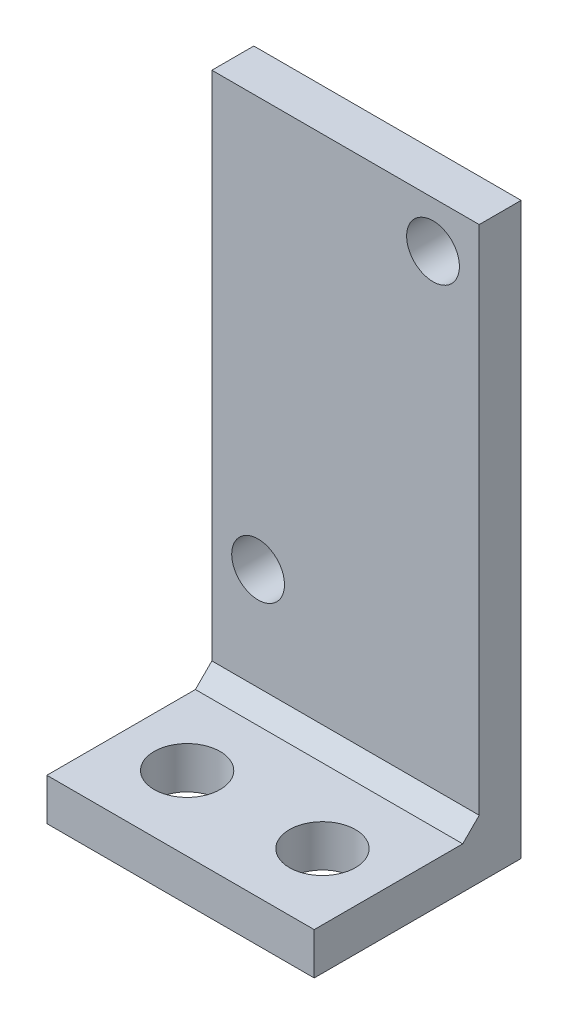
SolidWorks part; units mm, degrees
ref_plane "Front Plane" through (0, 0, 0) normal (0, 0, 1) x (1, 0, 0)
ref_plane "Top Plane" through (0, 0, 0) normal (0, 1, 0) x (1, 0, 0)
ref_plane "Right Plane" through (0, 0, 0) normal (1, 0, 0) x (0, 0, -1)
sketch "Sketch1" plane through (0, 0, 0) normal (0, 0, 1) x (1, 0, 0)
  line L1 (0, 0) -> (16.2, 0)
  line L2 (0, 0) -> (0, 34.54)
  line L3 (0, 34.54) -> (16.2, 34.54)
  line L4 (16.2, 0) -> (16.2, 34.54)
  dimension "D1" = 16.2
  dimension "D2" = 34.54
extrude "Boss-Extrude1" add sketch "Sketch1" along normal blind 2.54
sketch "Sketch2" plane through (0, 0, 2.54) normal (0, 0, 1) x (1, 0, 0)
  line L0 (16.2, 0) -> (16.2, 34.54) construction
  line L1 (0, 0) -> (16.2, 0)
  line L2 (0, 0) -> (0, 2.54)
  line L3 (0, 2.54) -> (16.2, 2.54)
  line L4 (16.2, 0) -> (16.2, 2.54)
  dimension "D1" = 2.54
extrude "Boss-Extrude2" add sketch "Sketch2" along normal blind 10
chamfer "Chamfer1" distance 1 angle 45 1 edges at (8.1, 2.54, 2.54)
sketch "Sketch4" plane through (0, 0, 0) normal (0, 0, -1) x (-1, 0, 0)
  line L0 (-16.2, 0) -> (-16.2, 34.54) construction
  line L1 (-16.2, 34.54) -> (0, 34.54) construction
  line L2 (0, 34.54) -> (0, 0) construction
  circle A0 centre (-13.4, 31.74) radius 1.6
  circle A1 centre (-2.8, 9.74) radius 1.6
  dimension "D1" = 3.2
  dimension "D2" = 2.8
  dimension "D3" = 2.8
  dimension "D4" = 2.8
  dimension "D5" = 22
extrude "Cut-Extrude1" cut sketch "Sketch4" against normal blind 2.54
sketch "Sketch5" plane through (0, 2.54, 0) normal (0, 1, 0) x (1, 0, 0)
  line L0 (16.2, -8.04) -> (0, -8.04) construction
  line L1 (16.2, -12.54) -> (16.2, -3.54) construction
  line L2 (0, -12.54) -> (0, -3.54) construction
  circle A0 centre (12.2, -8.04) radius 2
  circle A1 centre (4, -8.04) radius 2
  dimension "D1" = 4
extrude "Cut-Extrude2" cut sketch "Sketch5" against normal through all
